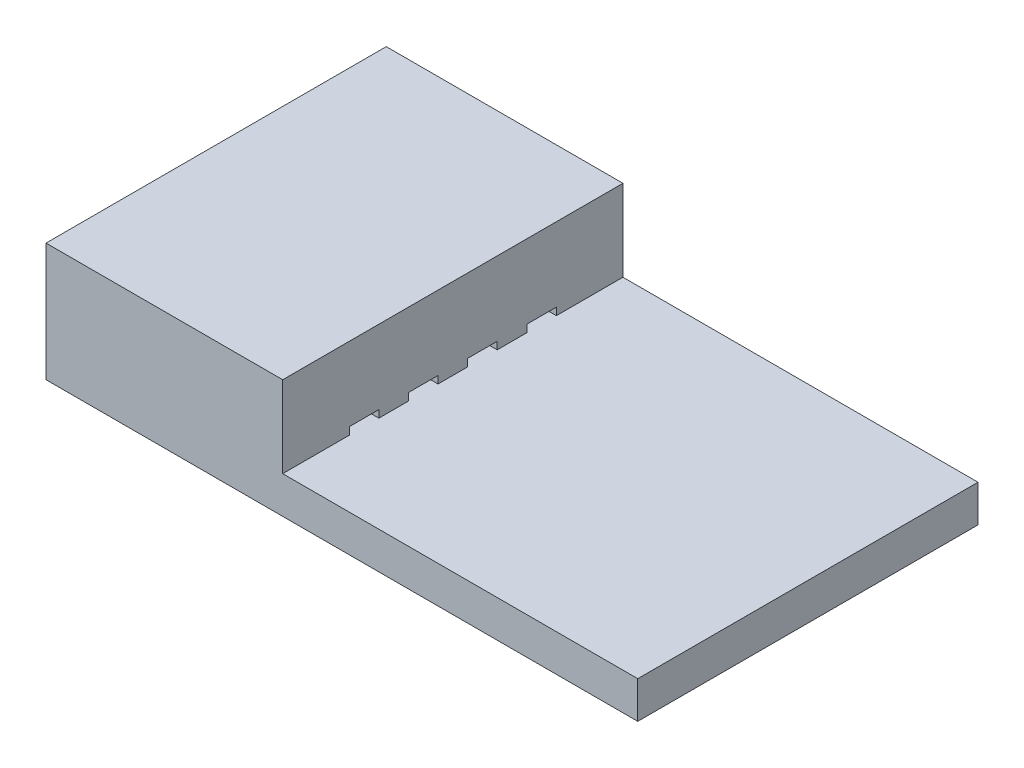
SolidWorks part; units mm, degrees
ref_plane "Front Plane" through (0, 0, 0) normal (0, 0, 1) x (1, 0, 0)
ref_plane "Top Plane" through (0, 0, 0) normal (0, 1, 0) x (1, 0, 0)
ref_plane "Right Plane" through (0, 0, 0) normal (1, 0, 0) x (0, 0, -1)
other "Configuration Table"
sketch "Insulator_body_sketch" plane through (0, 0, 0) normal (1, 0, 0) x (0, 0, -1)
  line L1 (-5.75, 2) -> (5.75, 2)
  line L2 (-5.75, 2) -> (-5.75, -2)
  line L3 (-5.75, -2) -> (5.75, -2)
  line L4 (5.75, 2) -> (5.75, -2)
  line L5 (-5.75, 2) -> (5.75, -2) construction
  line L6 (-5.75, -2) -> (5.75, 2) construction
  point P0 (0, 0)
  dimension "D1" = 11.5
  dimension "D2" = 4
extrude "Insulator_body" add sketch "Insulator_body_sketch" against normal blind 20
sketch "Insulator_tongue_sketch" plane through (0, 2, 0) normal (0, 1, 0) x (1, 0, 0)
  line L0 (-20, 5.75) -> (0, 5.75) construction
  line L1 (0, -5.75) -> (-12, -5.75)
  line L2 (0, -5.75) -> (0, 5.75)
  line L3 (0, 5.75) -> (-12, 5.75)
  line L4 (-12, -5.75) -> (-12, 5.75)
  dimension "D1" = 12
extrude "Insulator_tongue" cut sketch "Insulator_tongue_sketch" against normal offset from surface (2.75 mm away) 1.25 up to face at (-10, -2, 0)
sketch "Contact_slot_sketch" plane through (-12, 0, 0) normal (1, 0, 0) x (0, 0, -1)
  line L0 (0, -0.75) -> (0, 0) construction
  line L1 (5.75, -0.75) -> (-5.75, -0.75) construction
  line L3 (-3.5, -0.75) -> (-2.5, -0.75)
  line L4 (-3.5, -0.75) -> (-3.5, -0.5)
  line L5 (-3.5, -0.5) -> (-2.5, -0.5)
  line L6 (-2.5, -0.75) -> (-2.5, -0.5)
  dimension "D1" = 1
  dimension "D2" = 0.25
  dimension "D3" = 2.5
extrude "Contact_slot" cut sketch "Contact_slot_sketch" against normal through all
pattern_linear "Contact_slot_pattern" count 4 spacing 2 along (0, 0, -1) of "Contact_slot"
